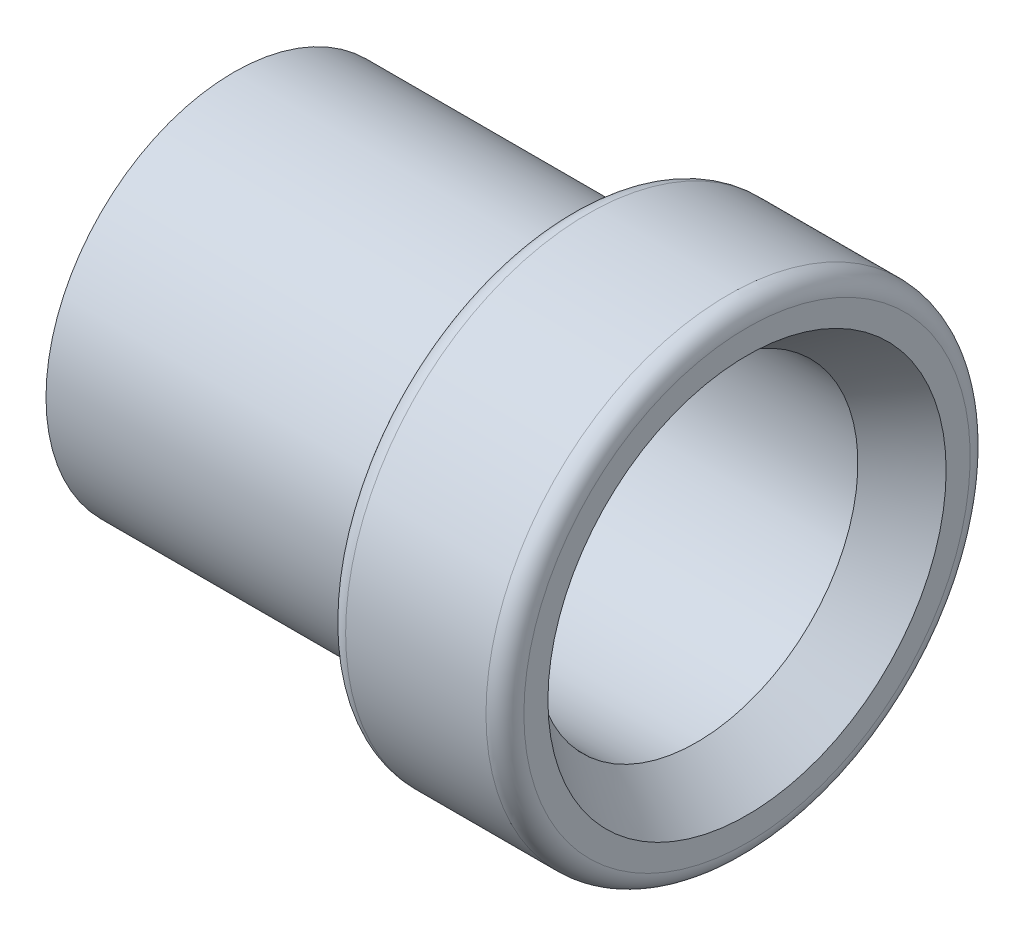
SolidWorks part; units mm, degrees
material "AISI 321 Annealed Stainless Steel (SS)"
ref_plane "Front Plane" through (0, 0, 0) normal (0, 0, 1) x (1, 0, 0)
ref_plane "Top Plane" through (0, 0, 0) normal (0, 1, 0) x (1, 0, 0)
ref_plane "Right Plane" through (0, 0, 0) normal (1, 0, 0) x (0, 0, -1)
sketch "Sketch1" plane through (0, 0, 0) normal (0, 0, 1) x (1, 0, 0)
  line L0 (-5.1562, 0) -> (5.1562, 0) construction
  line L1 (-5.1562, 3.2385) -> (4.145, 3.2385)
  line L2 (4.145, 3.2385) -> (5.1562, 4.0005)
  line L4 (5.1562, 4.0005) -> (5.1562, 4.4831)
  line L5 (4.7752, 4.8641) -> (1.9558, 4.8641)
  line L6 (1.5748, 4.4831) -> (1.5748, 3.7719)
  line L7 (1.5748, 3.7719) -> (-5.1562, 3.7719)
  line L8 (-5.1562, 3.2385) -> (-5.1562, 3.7719)
  arc A0 (5.1562, 4.4831) -> (4.7752, 4.8641) centre (4.7752, 4.4831) ccw
  arc A1 (1.9558, 4.8641) -> (1.5748, 4.4831) centre (1.9558, 4.4831) ccw
  point P12 (5.1562, 4.8641)
  point P15 (1.5748, 4.8641)
  dimension "D2" = 0.381
  dimension "D1" = 37
  dimension "M" = 10.3124
  dimension "G" = 9.7282
  dimension "J" = 3.5814
  dimension "B" = 6.477
  dimension "C" = 7.5438
  dimension "F" = 8.001
revolve "Revolve1" add sketch "Sketch1" angle 360 about L0
